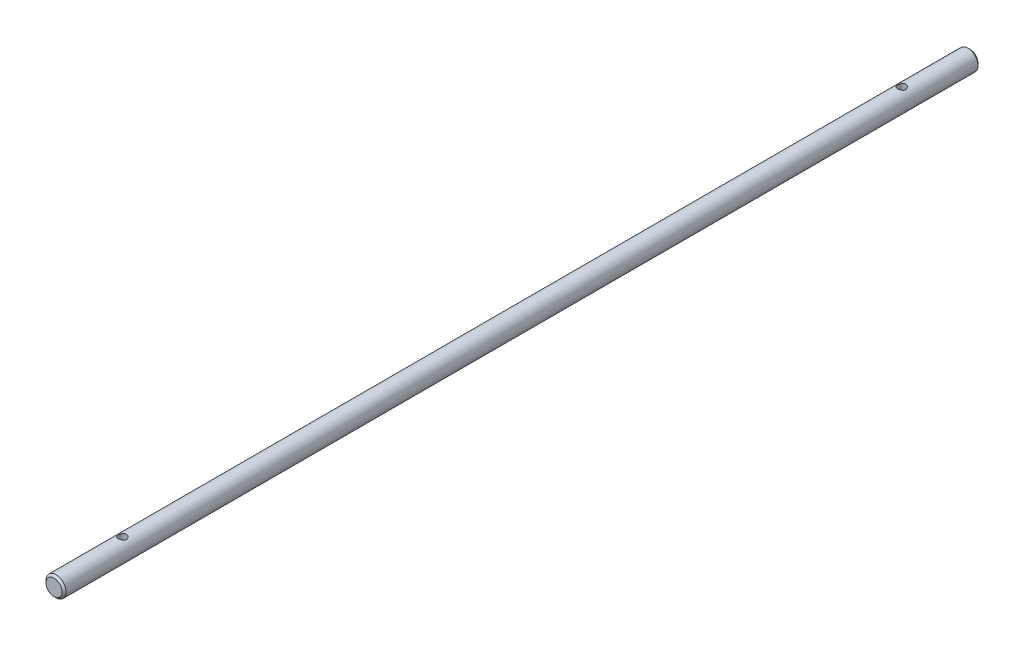
SolidWorks part; units mm, degrees
ref_plane "Plane1" through (0, 0, 0) normal (0, 0, 1) x (1, 0, 0)
ref_plane "Plane2" through (0, 0, 0) normal (0, 1, 0) x (1, 0, 0)
ref_plane "Plane3" through (0, 0, 0) normal (1, 0, 0) x (0, 0, -1)
sketch "Esquisse1" plane through (0, 0, 0) normal (0, 0, 1) x (1, 0, 0)
  circle A0 centre (0, 0) radius 2.5
  dimension "D1" = 5
extrude "Base-Extrusion" add sketch "Esquisse1" along normal blind 228
chamfer "Chanfrein1" distance 0.5 angle 45
sketch "Esquisse2" plane through (0, 0, 0) normal (0, 1, 0) x (1, 0, 0)
  line L0 (0, -227.5) -> (0, -0.5) construction
  line L1 (2, 0) -> (-2, 0) construction
  line L2 (-2, -228) -> (2, -228) construction
  circle A0 centre (0, -17) radius 1
  circle A1 centre (0, -211) radius 1
  dimension "D1" = 2
  dimension "D4" = 2
  dimension "D2" = 17
  dimension "D3" = 17
extrude "Enlèv. mat.-Extru.1" cut sketch "Esquisse2" against normal mid plane 100
